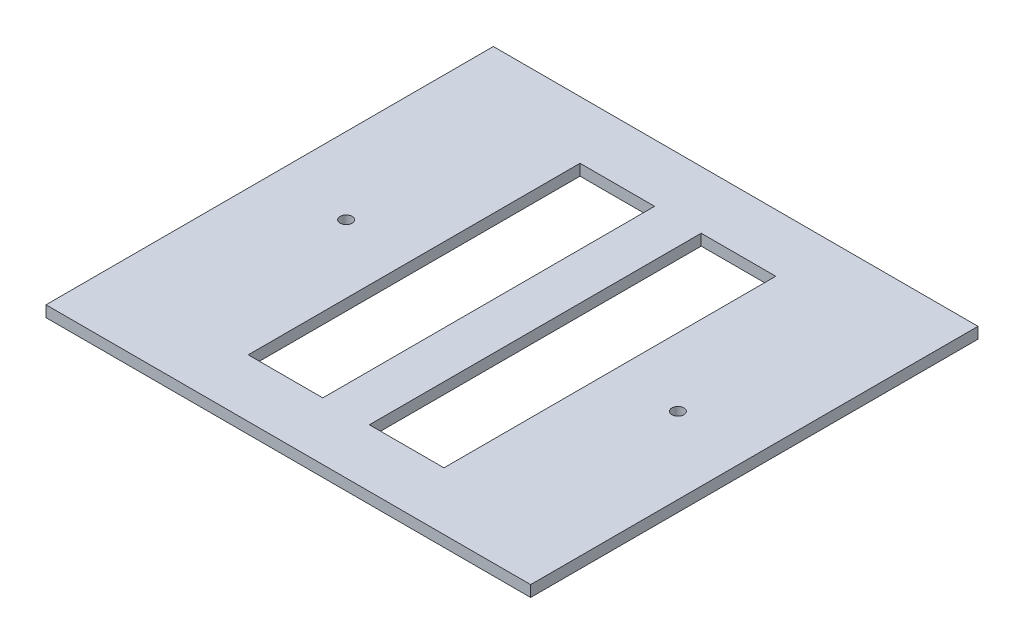
SolidWorks part; units mm, degrees
ref_plane "Front Plane" through (0, 0, 0) normal (0, 0, 1) x (1, 0, 0)
ref_plane "Top Plane" through (0, 0, 0) normal (0, 1, 0) x (1, 0, 0)
ref_plane "Right Plane" through (0, 0, 0) normal (1, 0, 0) x (0, 0, -1)
sketch "Sketch1" plane through (0, 0, 0) normal (0, 1, 0) x (1, 0, 0)
  line L1 (-65, -60) -> (65, -60)
  line L2 (-65, -60) -> (-65, 60)
  line L3 (-65, 60) -> (65, 60)
  line L4 (65, -60) -> (65, 60)
  line L5 (-65, -60) -> (65, 60) construction
  line L6 (-65, 60) -> (65, -60) construction
  point P0 (0, 0)
  dimension "D1" = 130
  dimension "D2" = 120
extrude "Boss-Extrude1" add sketch "Sketch1" along normal blind 3
sketch "Sketch2" plane through (0, 3, 0) normal (0, 1, 0) x (1, 0, 0)
  line L1 (-26.25, -44.5) -> (-6.25, -44.5)
  line L2 (-26.25, -44.5) -> (-26.25, 44.5)
  line L3 (-26.25, 44.5) -> (-6.25, 44.5)
  line L4 (-6.25, -44.5) -> (-6.25, 44.5)
  line L5 (-26.25, -44.5) -> (-6.25, 44.5) construction
  line L6 (-26.25, 44.5) -> (-6.25, -44.5) construction
  point P0 (-16.25, 0)
  point P5 (0, 0)
  dimension "D1" = 89
  dimension "D2" = 20
  dimension "D3" = 6.25
extrude "Cut-Extrude1" cut sketch "Sketch2" against normal through all both and the other way through all
mirror "Mirror1" about plane through (0, 0, 0) normal (1, 0, 0) of "Cut-Extrude1"
sketch "Sketch3" plane through (0, 3, 0) normal (0, 1, 0) x (1, 0, 0)
  circle A0 centre (44.5, 0) radius 1.6
  point P2 (0, 0)
  point P4 (0, 0)
  dimension "D1" = 3.2
  dimension "D2" = 44.5
extrude "Cut-Extrude2" cut sketch "Sketch3" against normal through all both and the other way through all
mirror "Mirror2" about plane through (0, 0, 0) normal (1, 0, 0) of "Cut-Extrude2"
